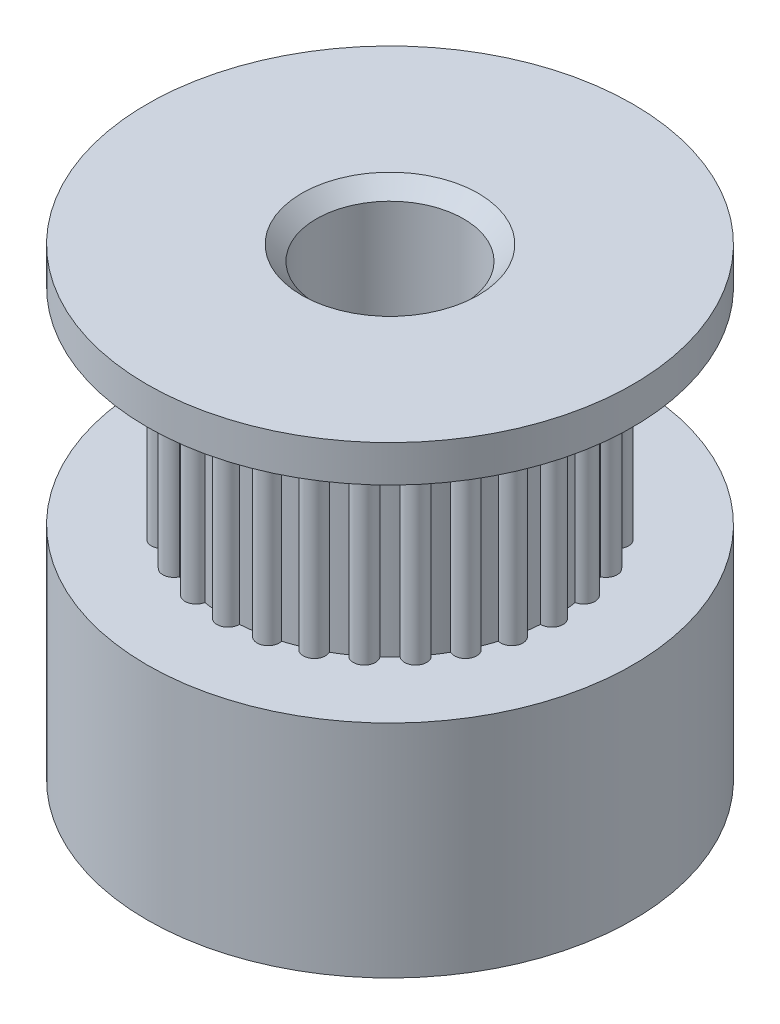
SolidWorks part; units mm, degrees
ref_plane "Front Plane" through (0, 0, 0) normal (0, 0, 1) x (1, 0, 0)
ref_plane "Top Plane" through (0, 0, 0) normal (0, 1, 0) x (1, 0, 0)
ref_plane "Right Plane" through (0, 0, 0) normal (1, 0, 0) x (0, 0, -1)
sketch "Sketch1" plane through (0, 0, 0) normal (0, 1, 0) x (1, 0, 0)
  circle A0 centre (0, 0) radius 8.382
  dimension "D1" = 16.764
extrude "Boss-Extrude1" add sketch "Sketch1" against normal blind 7.62
sketch "Sketch2" plane through (0, 0, 0) normal (0, 1, 0) x (1, 0, 0)
  circle A0 centre (0, 0) radius 5.969 construction
  circle A1 centre (0, 0) radius 5.588 construction
  arc A2 (-5.575, -0.3808) -> (-5.575, 0.3808) centre (-5.588, 0) cw
  circle A3 centre (0, 0) radius 5.588 construction
  arc A4 (-5.52, 0.8693) -> (-5.3505, 1.6118) centre (-5.4479, 1.2434) cw
  arc A6 (-5.1881, 2.0758) -> (-4.8577, 2.762) centre (-5.0346, 2.4245) cw
  arc A8 (-4.5961, 3.1783) -> (-4.1213, 3.7737) centre (-4.3689, 3.4841) cw
  arc A10 (-3.7737, 4.1213) -> (-3.1783, 4.5961) centre (-3.4841, 4.3689) cw
  arc A12 (-2.762, 4.8577) -> (-2.0758, 5.1881) centre (-2.4245, 5.0346) cw
  arc A14 (-1.6118, 5.3505) -> (-0.8693, 5.52) centre (-1.2434, 5.4479) cw
  arc A16 (-0.3808, 5.575) -> (0.3808, 5.575) centre (0, 5.588) cw
  circle A17 centre (0, 0) radius 5.588
  arc A18 (0.8693, 5.52) -> (1.6118, 5.3505) centre (1.2434, 5.4479) cw
  circle A19 centre (0, 0) radius 5.588
  arc A20 (2.0758, 5.1881) -> (2.762, 4.8577) centre (2.4245, 5.0346) cw
  circle A21 centre (0, 0) radius 5.588
  arc A22 (3.1783, 4.5961) -> (3.7737, 4.1213) centre (3.4841, 4.3689) cw
  circle A23 centre (0, 0) radius 5.588
  arc A24 (4.1213, 3.7737) -> (4.5961, 3.1783) centre (4.3689, 3.4841) cw
  circle A25 centre (0, 0) radius 5.588
  arc A26 (4.8577, 2.762) -> (5.1881, 2.0758) centre (5.0346, 2.4245) cw
  circle A27 centre (0, 0) radius 5.588 construction
  arc A28 (5.3505, 1.6118) -> (5.52, 0.8693) centre (5.4479, 1.2434) cw
  circle A29 centre (0, 0) radius 5.588
  arc A30 (5.575, 0.3808) -> (5.575, -0.3808) centre (5.588, 0) cw
  arc A32 (5.52, -0.8693) -> (5.3505, -1.6118) centre (5.4479, -1.2434) cw
  circle A33 centre (0, 0) radius 5.588
  arc A34 (5.1881, -2.0758) -> (4.8577, -2.762) centre (5.0346, -2.4245) cw
  arc A36 (4.5961, -3.1783) -> (4.1213, -3.7737) centre (4.3689, -3.4841) cw
  arc A38 (3.7737, -4.1213) -> (3.1783, -4.5961) centre (3.4841, -4.3689) cw
  circle A39 centre (0, 0) radius 5.588
  arc A40 (2.762, -4.8577) -> (2.0758, -5.1881) centre (2.4245, -5.0346) cw
  arc A42 (1.6118, -5.3505) -> (0.8693, -5.52) centre (1.2434, -5.4479) cw
  circle A43 centre (0, 0) radius 5.588
  arc A44 (0.3808, -5.575) -> (-0.3808, -5.575) centre (0, -5.588) cw
  arc A46 (-0.8693, -5.52) -> (-1.6118, -5.3505) centre (-1.2434, -5.4479) cw
  circle A47 centre (0, 0) radius 5.588
  arc A48 (-2.0758, -5.1881) -> (-2.762, -4.8577) centre (-2.4245, -5.0346) cw
  circle A49 centre (0, 0) radius 5.588
  arc A50 (-3.1783, -4.5961) -> (-3.7737, -4.1213) centre (-3.4841, -4.3689) cw
  circle A51 centre (0, 0) radius 5.588
  arc A52 (-4.1213, -3.7737) -> (-4.5961, -3.1783) centre (-4.3689, -3.4841) cw
  circle A53 centre (0, 0) radius 5.588
  arc A54 (-4.8577, -2.762) -> (-5.1881, -2.0758) centre (-5.0346, -2.4245) cw
  circle A55 centre (0, 0) radius 5.588
  arc A56 (-5.3505, -1.6118) -> (-5.52, -0.8693) centre (-5.4479, -1.2434) cw
  circle A57 centre (0, 0) radius 5.588 [skipped]
  circle A58 centre (0, 0) radius 5.588 [skipped]
  circle A59 centre (0, 0) radius 5.588 [skipped]
  circle A60 centre (0, 0) radius 5.588 [skipped]
  circle A61 centre (0, 0) radius 5.588 [skipped]
  circle A62 centre (0, 0) radius 5.588 [skipped]
  circle A63 centre (0, 0) radius 5.588 [skipped]
  circle A64 centre (0, 0) radius 5.588 [skipped]
  circle A65 centre (0, 0) radius 5.588 [skipped]
  circle A66 centre (0, 0) radius 5.588 [skipped]
  circle A67 centre (0, 0) radius 5.588 [skipped]
  point P117 (0, 0)
  dimension "D1" = 11.938
  dimension "D2" = 0.381
  dimension "D3" = 28
extrude "Boss-Extrude2" add sketch "Sketch2" along normal blind 7.112 contours A17 A8 | A17 A6 | A17 A4 | A17 A2 | A56 A55 | A54 A53 | A52 A51 | A48 A47 | A46 A43 | A40 A39 | A38 A33 | A36 A33 | A34 A33 | A30 A29 | A28 A25 | A26 A25 | A24 A23 | A22 A21 | A20 A19 | A18 A17 | A17 A16 | A17 A14 | A17 A12 | A17 A10 | A50 A49 | A44 A43 | A42 A39 | A32 A29 | A17 A55 A53 A51 A49 A47 A43 A39 A33 A29 A25 A23 A21 A19
sketch "Sketch3" plane through (0, 7.112, 0) normal (0, 1, 0) x (1, 0, 0)
  circle A0 centre (0, 0) radius 8.382 construction
  circle A1 centre (0, 0) radius 8.382
extrude "Boss-Extrude3" add sketch "Sketch3" along normal blind 1.27
sketch "Sketch4" plane through (0, -7.62, 0) normal (0, -1, 0) x (1, 0, 0)
  circle A0 centre (0, 0) radius 2.54
  point P3 (0, 0)
  dimension "D1" = 5.08
extrude "Cut-Extrude1" cut sketch "Sketch4" against normal through all both and the other way through all
chamfer "Chamfer1" distance 0.508 angle 45 2 edges at (0, 8.382, -2.54) (0, -7.62, 2.54)
sketch "Sketch5" plane through (0, 0, 0) normal (1, 0, 0) x (0, 0, -1)
  line L0 (-8.382, -3.81) -> (0, -3.81) construction
  line L1 (-8.382, 0) -> (-8.382, -7.62) construction
  circle A0 centre (0, -3.81) radius 1.651
  point P3 (0, 0)
  dimension "D1" = 3.302
extrude "Cut-Extrude2" cut sketch "Sketch5" against normal through all
